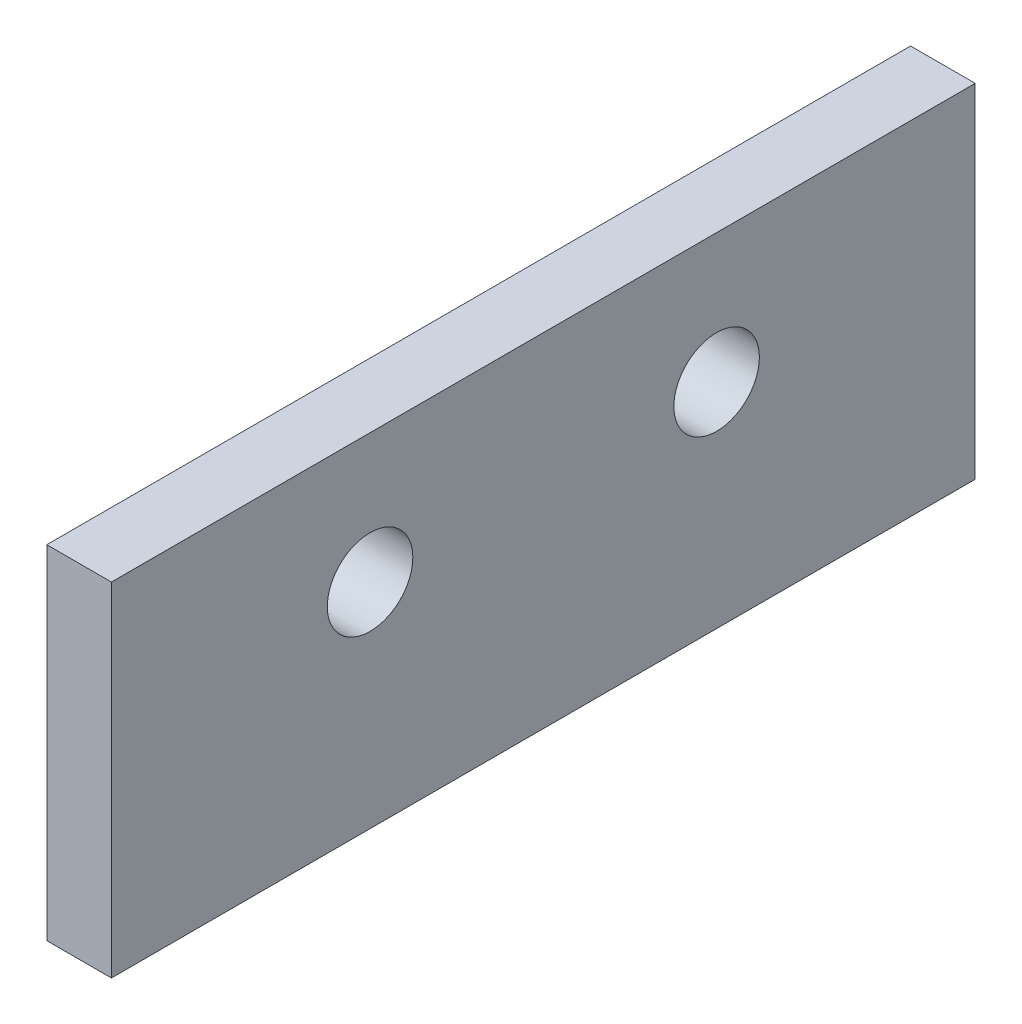
SolidWorks part; units mm, degrees
material "Silicon Rubber"
ref_plane "Front Plane" through (0, 0, 0) normal (0, 0, 1) x (1, 0, 0)
ref_plane "Top Plane" through (0, 0, 0) normal (0, 1, 0) x (1, 0, 0)
ref_plane "Right Plane" through (0, 0, 0) normal (1, 0, 0) x (0, 0, -1)
sketch "Sketch1" plane through (0, 0, 0) normal (1, 0, 0) x (0, 0, -1)
  line L13 (-21.209, -8.4201) -> (21.209, -8.4201)
  line L14 (-21.209, -8.4201) -> (-21.209, 8.4201)
  line L15 (-21.209, 8.4201) -> (21.209, 8.4201)
  line L16 (21.209, -8.4201) -> (21.209, 8.4201)
  line L17 (-21.209, -8.4201) -> (21.209, 8.4201) construction
  line L18 (-21.209, 8.4201) -> (21.209, -8.4201) construction
  point P0 (0, 0)
  dimension "D2" = 42.418
  dimension "D1" = 16.8402
extrude "Boss-Extrude1" add sketch "Sketch1" along normal blind 3.175
sketch "Sketch3" plane through (3.175, 0, 0) normal (1, 0, 0) x (0, 0, -1)
  line L7 (-21.209, 8.4201) -> (-21.209, -4.2799) construction
  line L8 (-21.209, 8.4201) -> (-21.209, -8.4201) construction
  line L9 (-21.209, 2.0701) -> (21.209, 2.0701) construction
  line L10 (21.209, -8.4201) -> (21.209, 8.4201) construction
  circle A2 centre (-8.509, 2.0701) radius 2.1
  circle A3 centre (8.509, 2.0701) radius 2.1
  dimension "D1" = 12.7
  dimension "D4" = 4.2
  dimension "D5" = 12.7
  dimension "D3" = 12.7
extrude "Cut-Extrude1" cut sketch "Sketch3" against normal through all
